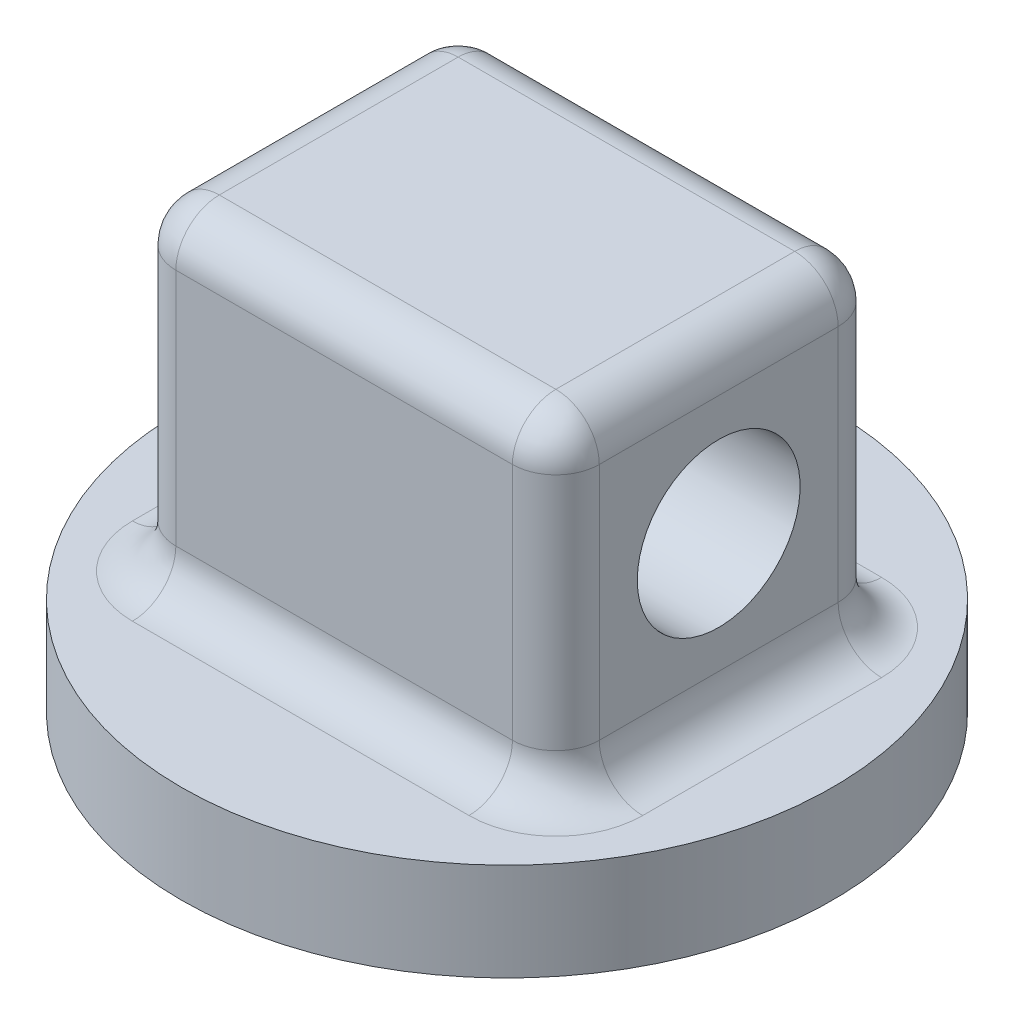
SolidWorks part; units mm, degrees
material "ABS"
ref_plane "Front Plane" through (0, 0, 0) normal (0, 0, 1) x (1, 0, 0)
ref_plane "Top Plane" through (0, 0, 0) normal (0, 1, 0) x (1, 0, 0)
ref_plane "Right Plane" through (0, 0, 0) normal (1, 0, 0) x (0, 0, -1)
sketch "Sketch1" plane through (0, 0, 0) normal (0, 1, 0) x (1, 0, 0)
  circle A0 centre (0, 0) radius 25.4
  dimension "D1" = 50.8
extrude "Boss-Extrude1" add sketch "Sketch1" along normal blind 7.62
sketch "Sketch2" plane through (0, 7.62, 0) normal (0, 1, 0) x (1, 0, 0)
  line L1 (-16.51, 12.7) -> (16.51, 12.7)
  line L2 (-16.51, 12.7) -> (-16.51, -12.7)
  line L3 (-16.51, -12.7) -> (16.51, -12.7)
  line L4 (16.51, 12.7) -> (16.51, -12.7)
  line L5 (-16.51, 12.7) -> (16.51, -12.7) construction
  line L6 (-16.51, -12.7) -> (16.51, 12.7) construction
  point P0 (0, 0)
  dimension "D1" = 25.4
  dimension "D2" = 33.02
extrude "Boss-Extrude2" add sketch "Sketch2" along normal blind 25.4
sketch "Sketch4" plane through (-16.51, 0, 0) normal (-1, 0, 0) x (0, 0, 1)
  circle A0 centre (0, 20.32) radius 6.35
  dimension "D1" = 12.7
extrude "Cut-Extrude1" cut sketch "Sketch4" against normal through all both
scale "Scale1" scale about centroid uniform scaling yes scale factor 3
sketch "Sketch5" plane through (0, 0, 0) normal (0, 0, 1) x (1, 0, 0)
  line L0 (-76.2, -2.1196) -> (-76.2, -24.9796) construction
  line L1 (-80.9473, -7.1996) -> (-71.4527, -7.1996)
  line L2 (-80.9473, -7.1996) -> (-80.9473, -19.8996)
  line L3 (-80.9473, -19.8996) -> (-71.4527, -19.8996)
  line L4 (-71.4527, -7.1996) -> (-71.4527, -19.8996)
  line L5 (-80.9473, -7.1996) -> (-71.4527, -19.8996) construction
  line L6 (-80.9473, -19.8996) -> (-71.4527, -7.1996) construction
  point P0 (-76.2, -13.5496)
  dimension "D1" = 12.7
ref_point "Point1"
fillet "Fillet1" radius 10.16 12 edges at (-49.53, -2.1196, 0) (49.53, -2.1196, 0) (49.53, 35.9804, -38.1) (-49.53, 35.9804, -38.1) (0, -2.1196, -38.1) (-49.53, 35.9804, 38.1) (49.53, 35.9804, 38.1) (0, -2.1196, 38.1) (0, 74.0804, 38.1) (-49.53, 74.0804, 0) (0, 74.0804, -38.1) (49.53, 74.0804, 0)
